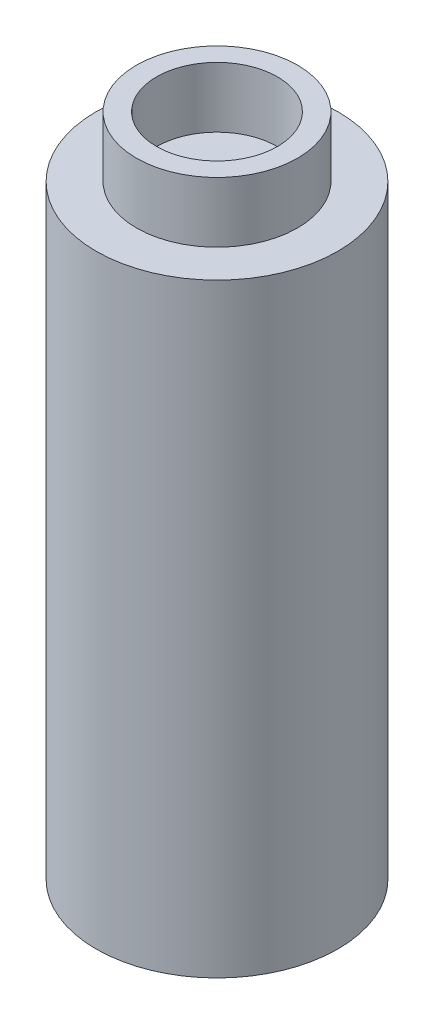
SolidWorks part; units mm, degrees
material "1060 Alloy"
ref_plane "Front Plane" through (0, 0, 0) normal (0, 0, 1) x (1, 0, 0)
ref_plane "Top Plane" through (0, 0, 0) normal (0, 1, 0) x (1, 0, 0)
ref_plane "Right Plane" through (0, 0, 0) normal (1, 0, 0) x (0, 0, -1)
sketch "Sketch2" plane through (0, 0, 0) normal (0, 1, 0) x (1, 0, 0)
  circle A0 centre (0, 0) radius 6
  dimension "D1" = 12
extrude "Boss-Extrude1" add sketch "Sketch2" along normal blind 30
sketch "Sketch3" plane through (0, 30, 0) normal (0, 1, 0) x (1, 0, 0)
  circle A0 centre (0, 0) radius 4
  dimension "D1" = 8
extrude "Boss-Extrude2" add sketch "Sketch3" along normal blind 3
sketch "Sketch4" plane through (0, 33, 0) normal (0, 1, 0) x (1, 0, 0)
  circle A0 centre (0, 0) radius 3
  dimension "D1" = 6
extrude "Cut-Extrude1" cut sketch "Sketch4" against normal blind 3
